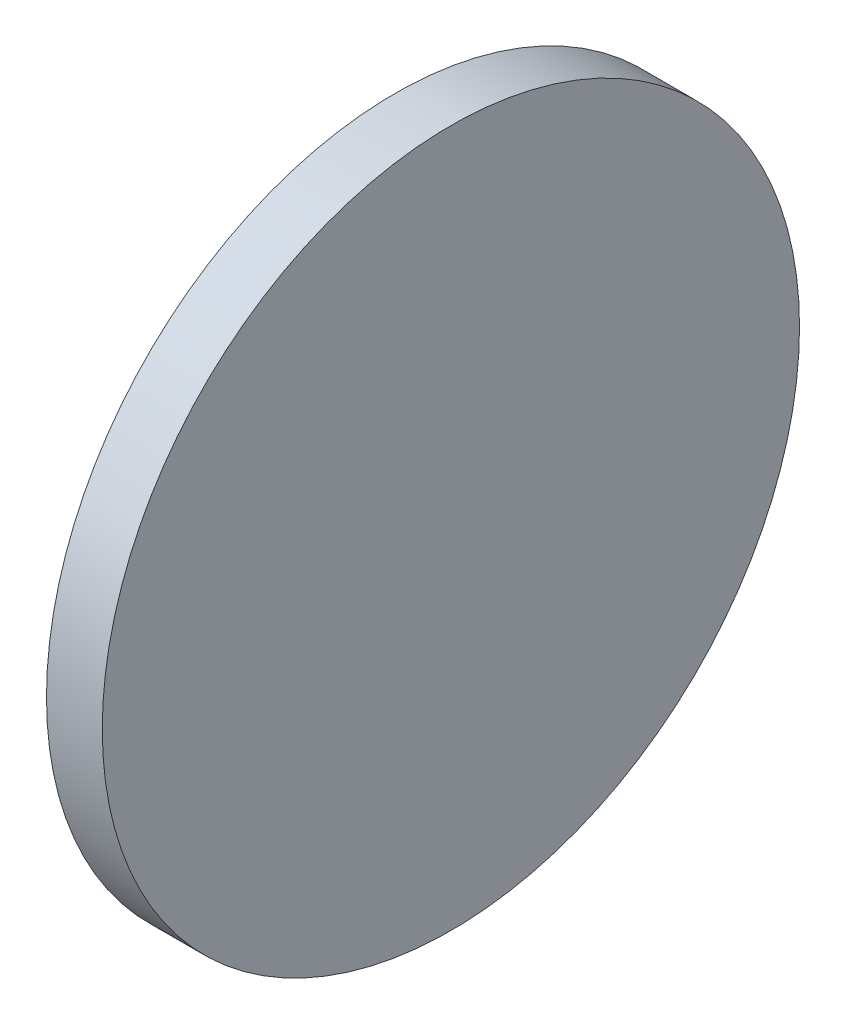
SolidWorks part; units mm, degrees
ref_plane "前视基准面" through (0, 0, 0) normal (0, 0, 1) x (1, 0, 0)
ref_plane "上视基准面" through (0, 0, 0) normal (0, 1, 0) x (1, 0, 0)
ref_plane "右视基准面" through (0, 0, 0) normal (1, 0, 0) x (0, 0, -1)
sketch "草图1" plane through (0, 0, 0) normal (0, 0, 1) x (1, 0, 0)
  line L0 (254.0008, 77.2932) -> (269.054, 77.2932) construction
  line L1 (260.2862, 77.2932) -> (260.2862, 89.7932)
  line L2 (260.2862, 89.7932) -> (262.2862, 89.7932)
  line L3 (262.2862, 89.7932) -> (262.2862, 77.2932)
  line L4 (262.2862, 77.2932) -> (260.2862, 77.2932)
  dimension "D1" = 12.5
  dimension "D2" = 2
revolve "旋转1" add sketch "草图1" angle 360 about L0
